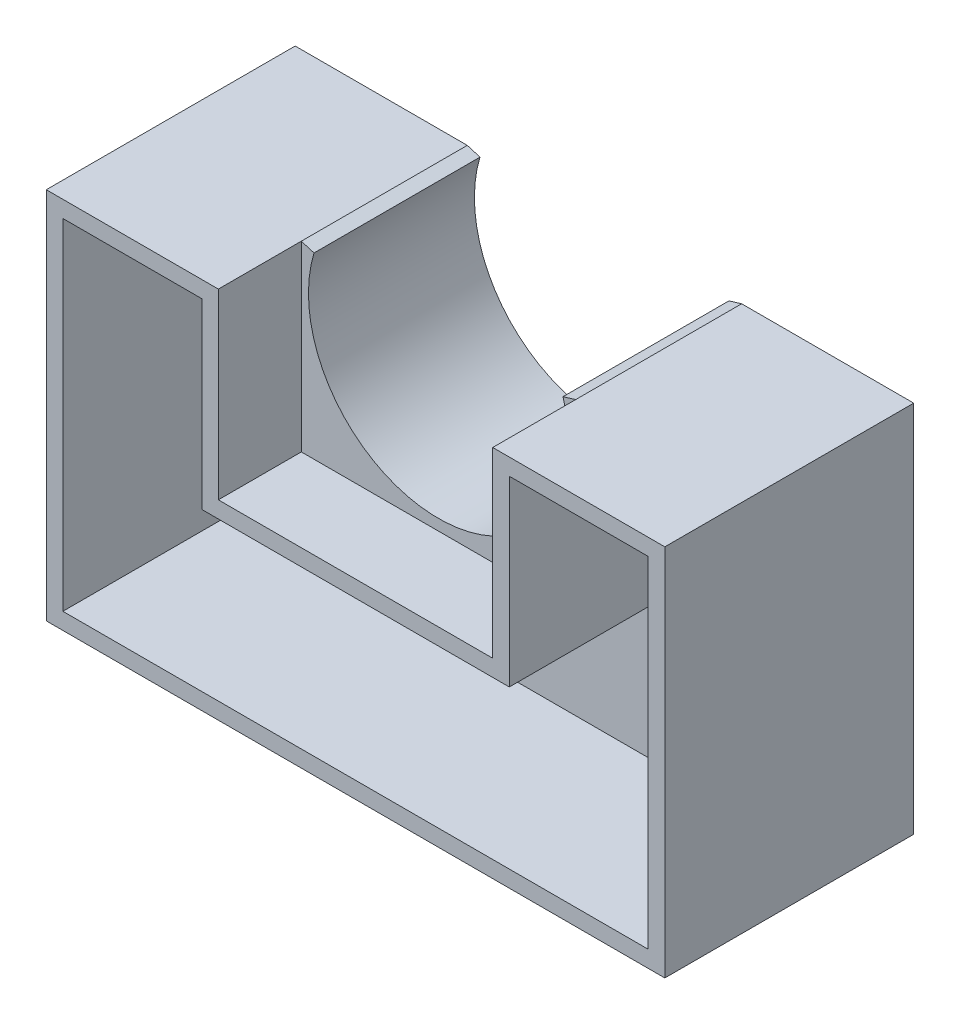
SolidWorks part; units mm, degrees
ref_plane "Front Plane" through (0, 0, 0) normal (0, 0, 1) x (1, 0, 0)
ref_plane "Top Plane" through (0, 0, 0) normal (0, 1, 0) x (1, 0, 0)
ref_plane "Right Plane" through (0, 0, 0) normal (1, 0, 0) x (0, 0, -1)
sketch "Sketch1" plane through (0, 0, 0) normal (0, 0, 1) x (1, 0, 0)
  line L0 (10.4991, 3.1773) -> (9.5267, 2.8831)
  line L1 (-9.5267, 2.8831) -> (-10.4991, 3.1773)
  line L2 (10.9694, 0) -> (10.9694, -19.05)
  line L3 (10.9694, -19.05) -> (23.6694, -19.05)
  line L4 (23.6694, -19.05) -> (23.6694, -25.4)
  line L5 (23.6694, -25.4) -> (-23.6694, -25.4)
  line L6 (-23.6694, -25.4) -> (-23.6694, -19.05)
  line L7 (-23.6694, -19.05) -> (-10.9694, -19.05)
  line L8 (-10.9694, -19.05) -> (-10.9694, 0)
  arc A0 (-9.5267, 2.8831) -> (9.5267, 2.8831) centre (0, 0) ccw
  arc A1 (10.9694, 0) -> (10.4991, 3.1773) centre (0, 0) ccw
  arc A2 (-10.4991, 3.1773) -> (-10.9694, 0) centre (0, 0) ccw
  point P14 (0, 0)
  dimension "D1" = 25.4
  dimension "D2" = 9.9534
  dimension "D3" = 10.9694
  dimension "D4" = 10.9694
  dimension "D5" = 19.05
  dimension "D6" = 19.05
  dimension "D7" = 23.6694
  dimension "D8" = 23.6694
extrude "Boss-Extrude1" add sketch "Sketch1" along normal blind 12.7
sketch "Sketch2" plane through (0, -19.05, 0) normal (0, 1, 0) x (1, 0, 0)
  line L4 (23.6694, 0) -> (10.9694, 0)
  line L5 (10.9694, 0) -> (10.9694, -12.7)
  line L6 (10.9694, -12.7) -> (23.6694, -12.7)
  line L7 (23.6694, -12.7) -> (23.6694, 0)
  line L8 (23.6694, 0) -> (10.9694, 0)
  line L9 (10.9694, 0) -> (10.9694, -12.7)
  line L10 (10.9694, -12.7) -> (23.6694, -12.7)
  line L11 (23.6694, -12.7) -> (23.6694, 0)
  dimension "D1" = 0
extrude "Boss-Extrude2" add sketch "Sketch2" along normal up to vertex (22.2274 mm away)
sketch "Sketch3" plane through (0, 0, 0) normal (0, 0, -1) x (-1, 0, 0)
  line L0 (-10.9694, 0) -> (-10.9694, 3.1773)
  line L1 (-10.4991, 3.1773) -> (-10.9694, 3.1773)
  arc A0 (-10.4991, 3.1773) -> (-10.9694, 0) centre (0, 0) ccw construction
  arc A1 (-10.4991, 3.1773) -> (-10.9694, 0) centre (0, 0) ccw
extrude "Boss-Extrude3" add sketch "Sketch3" against normal through all
sketch "Sketch4" plane through (0, -19.05, 0) normal (0, 1, 0) x (1, 0, 0)
  line L4 (-10.9694, 0) -> (-23.6694, 0)
  line L5 (-23.6694, 0) -> (-23.6694, -12.7)
  line L6 (-23.6694, -12.7) -> (-10.9694, -12.7)
  line L7 (-10.9694, -12.7) -> (-10.9694, 0)
  line L8 (-10.9694, 0) -> (-23.6694, 0)
  line L9 (-23.6694, 0) -> (-23.6694, -12.7)
  line L10 (-23.6694, -12.7) -> (-10.9694, -12.7)
  line L11 (-10.9694, -12.7) -> (-10.9694, 0)
  dimension "D1" = 0
extrude "Boss-Extrude4" add sketch "Sketch4" along normal up to vertex (22.2274 mm away)
sketch "Sketch5" plane through (0, 0, 0) normal (0, 0, -1) x (-1, 0, 0)
  line L0 (10.9694, 3.1773) -> (10.9694, 0) construction
  line L1 (10.9694, 3.1773) -> (10.9694, 0)
  line L2 (10.9694, 3.1773) -> (10.4991, 3.1773)
  arc A0 (10.9694, 0) -> (10.4991, 3.1773) centre (0, 0) ccw construction
  arc A1 (10.9694, 0) -> (10.4991, 3.1773) centre (0, 0) ccw
extrude "Boss-Extrude5" add sketch "Sketch5" against normal through all
sketch "Sketch6" plane through (0, 0, 12.7) normal (0, 0, 1) x (1, 0, 0)
  line L0 (-23.6694, 3.1773) -> (-23.6694, -25.4)
  line L1 (-23.6694, -25.4) -> (23.6694, -25.4)
  line L2 (23.6694, -25.4) -> (23.6694, 3.1773)
  line L3 (23.6694, 3.1773) -> (10.4991, 3.1773)
  line L4 (10.4991, 3.1773) -> (10.4991, -10.7927)
  line L5 (-23.6694, 3.1773) -> (-10.4991, 3.1773)
  line L6 (-10.4991, 3.1773) -> (-10.4991, -10.7927)
  line L7 (-10.4991, -10.7927) -> (10.4991, -10.7927)
  dimension "D1" = 13.97
extrude "Boss-Extrude6" add sketch "Sketch6" along normal blind 6.35
sketch "Sketch7" plane through (0, 0, 19.05) normal (0, 0, 1) x (1, 0, 0)
  line L16 (-11.7691, 1.9073) -> (-22.3994, 1.9073)
  line L17 (-22.3994, 1.9073) -> (-22.3994, -24.13)
  line L18 (-22.3994, -24.13) -> (22.3994, -24.13)
  line L19 (22.3994, -24.13) -> (22.3994, 1.9073)
  line L20 (22.3994, 1.9073) -> (11.7691, 1.9073)
  line L21 (11.7691, 1.9073) -> (11.7691, -12.0627)
  line L22 (11.7691, -12.0627) -> (-11.7691, -12.0627)
  line L23 (-11.7691, -12.0627) -> (-11.7691, 1.9073)
  line L24 (-11.7691, 1.9073) -> (-22.3994, 1.9073)
  line L25 (-22.3994, 1.9073) -> (-22.3994, -24.13)
  line L26 (-22.3994, -24.13) -> (22.3994, -24.13)
  line L27 (22.3994, -24.13) -> (22.3994, 1.9073)
  line L28 (22.3994, 1.9073) -> (11.7691, 1.9073)
  line L29 (11.7691, 1.9073) -> (11.7691, -12.0627)
  line L30 (11.7691, -12.0627) -> (-11.7691, -12.0627)
  line L31 (-11.7691, -12.0627) -> (-11.7691, 1.9073)
  dimension "D1" = 1.27
extrude "Cut-Extrude1" cut sketch "Sketch7" against normal blind 12.7
sketch "Sketch9" plane through (0, 0, 0) normal (0, 0, -1) x (-1, 0, 0)
  line L1 (-12.7, -2.54) -> (-22.86, -2.54)
  line L2 (-12.7, -2.54) -> (-12.7, 2.54)
  line L3 (-12.7, 2.54) -> (-22.86, 2.54)
  line L4 (-22.86, -2.54) -> (-22.86, 2.54)
  line L5 (-12.7, -2.54) -> (-22.86, 2.54) construction
  line L6 (-12.7, 2.54) -> (-22.86, -2.54) construction
  line L7 (2.54, -22.86) -> (-2.54, -22.86)
  line L8 (2.54, -22.86) -> (2.54, -12.7)
  line L9 (2.54, -12.7) -> (-2.54, -12.7)
  line L10 (-2.54, -22.86) -> (-2.54, -12.7)
  line L11 (2.54, -22.86) -> (-2.54, -12.7) construction
  line L12 (2.54, -12.7) -> (-2.54, -22.86) construction
  point P0 (-17.78, 0)
  point P5 (0, -17.78)
  point P10 (0.4869, -21.2624)
  point P11 (0, -19.461)
  point P12 (0.8763, -19.4366)
  point P14 (-20.3897, -2.7276)
  point P15 (-20.4481, 0)
  point P16 (0, 0)
  point P17 (-17.7022, 0)
  point P18 (0, 0)
  dimension "D1" = 5.08
  dimension "D2" = 10.16
  dimension "D3" = 5.08
  dimension "D4" = 10.16
  dimension "D5" = 17.78
  dimension "D6" = 17.78
extrude "Cut-Extrude2" cut sketch "Sketch9" against normal blind 2
